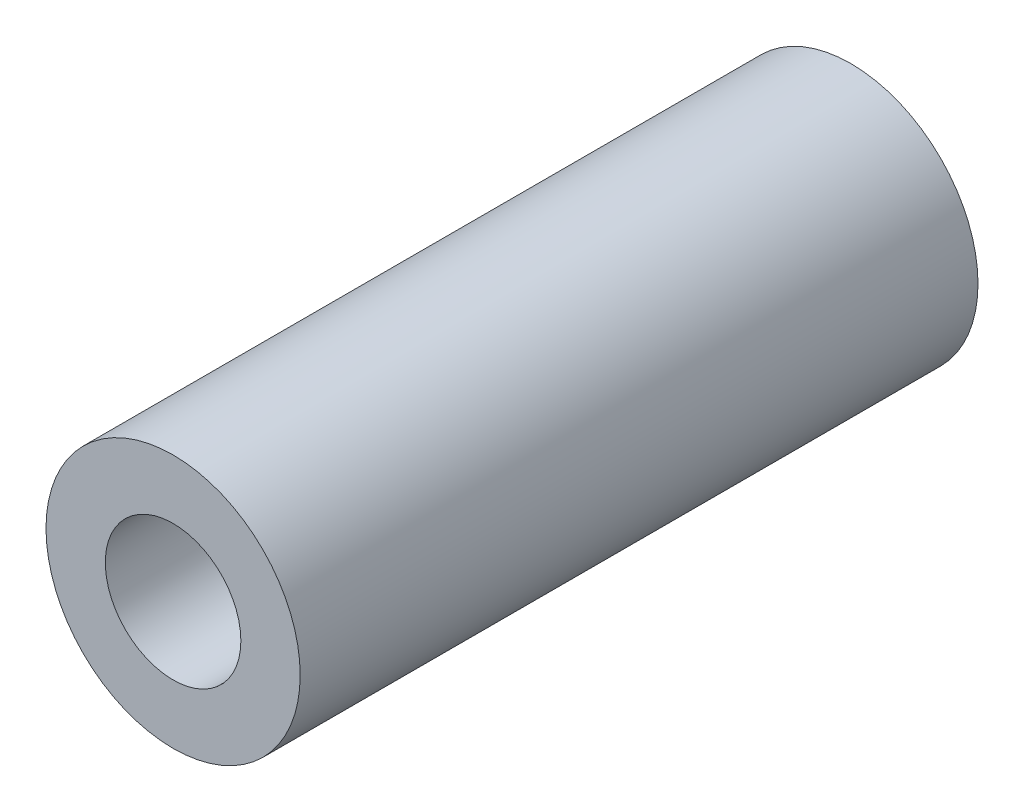
SolidWorks part; units mm, degrees
ref_plane "正面" through (0, 0, 0) normal (0, 0, 1) x (1, 0, 0)
ref_plane "平面" through (0, 0, 0) normal (0, 1, 0) x (1, 0, 0)
ref_plane "右側面" through (0, 0, 0) normal (1, 0, 0) x (0, 0, -1)
sketch "ｽｹｯﾁ1" plane through (0, 0, 0) normal (0, 0, 1) x (1, 0, 0)
  circle A0 centre (0, 0) radius 3
  circle A1 centre (0, 0) radius 1.6
  dimension "D1" = 6
  dimension "D2" = 3.2
extrude "ﾎﾞｽ - 押し出し1" add sketch "ｽｹｯﾁ1" along normal blind 16
